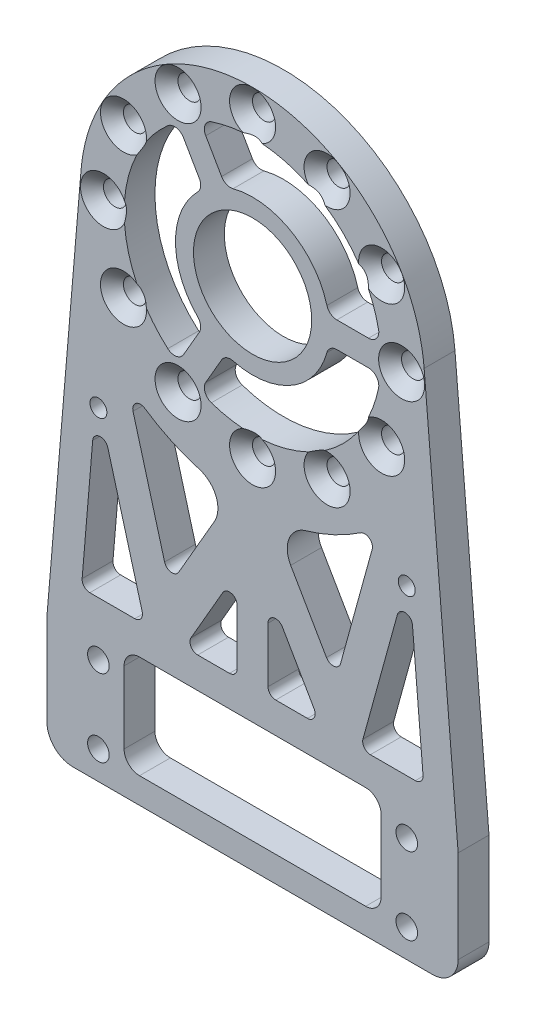
SolidWorks part; units mm, degrees
material "Thornel Mat VMA"
ref_plane "前视基准面" through (0, 0, 0) normal (0, 0, 1) x (1, 0, 0)
ref_plane "上视基准面" through (0, 0, 0) normal (0, 1, 0) x (1, 0, 0)
ref_plane "右视基准面" through (0, 0, 0) normal (1, 0, 0) x (0, 0, -1)
sketch "草图1" plane through (0, 0, 0) normal (0, 0, 1) x (1, 0, 0)
  line L0 (-40, 10) -> (-33.381, 88.3211)
  line L1 (-40, 10) -> (40, 10)
  line L2 (-40, 10) -> (-40, -10)
  line L3 (-40, -10) -> (40, -10)
  line L4 (40, 10) -> (40, -10)
  line L5 (-40, 10) -> (40, -10) construction
  line L6 (-40, -10) -> (40, 10) construction
  line L7 (-30, 7.5) -> (30, 7.5) construction
  line L8 (-30, 7.5) -> (-30, -7.5) construction
  line L9 (-30, -7.5) -> (30, -7.5) construction
  line L10 (30, 7.5) -> (30, -7.5) construction
  line L11 (-30, 7.5) -> (30, -7.5) construction
  line L12 (-30, -7.5) -> (30, 7.5) construction
  line L13 (33.381, 88.3211) -> (40, 10)
  circle A0 centre (0, 85.5) radius 33.5
  circle A1 centre (-30, -7.5) radius 2.1
  circle A2 centre (30, -7.5) radius 2.1
  circle A3 centre (30, 7.5) radius 2.1
  circle A4 centre (-30, 7.5) radius 2.1
  circle A5 centre (0, 85.5) radius 25
  point P0 (0, 0)
  point P6 (0, 0)
  dimension "D4" = 67
  dimension "D6" = 4.2
  dimension "D9" = 50
  dimension "D1" = 60
  dimension "D2" = 15
  dimension "D3" = 80
  dimension "D5" = 93
  dimension "D7" = 2
  dimension "D8" = 2
extrude "凸台-拉伸1" add sketch "草图1" along normal blind 6 contours A0 A5 | A0 L0 L1 L13 | L4 L1 L2 L3 A4 A3 A2 A1
sketch "草图3" plane through (0, 0, 6) normal (0, 0, 1) x (1, 0, 0)
  circle A0 centre (0, 85.5) radius 29 construction
  circle A1 centre (0, 114.5) radius 2.05
  circle A2 centre (14.5, 110.6147) radius 2.05
  circle A3 centre (25.1147, 100) radius 2.05
  circle A4 centre (29, 85.5) radius 2.05
  circle A5 centre (25.1147, 71) radius 2.05
  circle A6 centre (14.5, 60.3853) radius 2.05
  circle A7 centre (0, 56.5) radius 2.05
  circle A8 centre (-14.5, 60.3853) radius 2.05
  circle A9 centre (-25.1147, 71) radius 2.05
  circle A10 centre (-29, 85.5) radius 2.05
  circle A11 centre (-25.1147, 100) radius 2.05
  circle A12 centre (-14.5, 110.6147) radius 2.05
  point P29 (0, 85.5)
  dimension "D1" = 58
  dimension "D2" = 4.1
  dimension "D3" = 12
extrude "切除-拉伸1" cut sketch "草图3" against normal through all
sketch "草图4" plane through (0, 0, 6) normal (0, 0, 1) x (1, 0, 0)
  line L1 (-14.6024, 105.7921) -> (-7.7775, 93.9711)
  line L2 (-10.2723, 108.2921) -> (-3.4474, 96.4711)
  line L5 (24.8747, 83) -> (11.225, 83)
  line L6 (24.8747, 88) -> (11.225, 88)
  line L7 (-14.6024, 65.2079) -> (-7.7775, 77.0289)
  line L8 (-10.2723, 62.7079) -> (-3.4474, 74.5289)
  circle A0 centre (0, 85.5) radius 11.5
  arc A1 (-9.5602, 97.0587) -> (-9.5602, 73.9413) centre (0, 85.5) ccw
  circle A2 centre (0, 85.5) radius 25
  arc A3 (14.7902, 88) -> (-5.23, 99.5587) centre (0, 85.5) ccw
  arc A4 (-5.23, 71.4413) -> (14.7902, 83) centre (0, 85.5) ccw
  point P24 (0, 85.5)
  circle M13 centre (0, 85.5) radius 25
  dimension "D1" = 23
  dimension "D2" = 50
  dimension "D6" = 30
  dimension "D3" = 5
  dimension "D5" = 3
extrude "凸台-拉伸2" add sketch "草图4" against normal up to surface (6 mm away) separate body contours A0 L2 L1 M13 | A0 L5 L6 M13 | A0 L7 L8 M13 | L1 A1 L7 A0 | L8 A4 L5 A0 | L6 A3 L2 A0 up to face at (-23.0647, 71, 0)
combine bodies "组合1" operation type add bodies to combine 108 107
fillet "圆角1" radius 2 12 edges at (14.7902, 88, 3) (-5.23, 99.5587, 3) (24.8747, 88, 3) (-5.23, 71.4413, 3) (14.7902, 83, 3) (24.8747, 83, 3) (-10.2723, 62.7079, 3) (-10.2723, 108.2921, 3) (-9.5602, 73.9413, 3) (-14.6024, 65.2079, 3) (-9.5602, 97.0587, 3) (-14.6024, 105.7921, 3)
sketch "草图5" plane through (0, 0, 6) normal (0, 0, 1) x (1, 0, 0)
  line L1 (-40, -10) -> (40, -10)
  line L2 (-40, -10) -> (-40, -13)
  line L3 (-40, -13) -> (40, -13)
  line L4 (40, -10) -> (40, -13)
  dimension "D1" = 3
extrude "凸台-拉伸3" add sketch "草图5" against normal up to surface (6 mm away) up to face at (7.1078, 73.189, 0)
fillet "圆角2" radius 5 2 edges at (40, -13, 3) (-40, -13, 3)
sketch "草图6" plane through (0, 0, 0) normal (0, 0, -1) x (-1, 0, 0)
  line L0 (-39.3239, 18) -> (39.3239, 18)
  line L1 (-30, 7.5) -> (30, 7.5) construction
  line L2 (-30, 7.5) -> (-30, -7.5) construction
  line L3 (-30, -7.5) -> (30, -7.5) construction
  line L4 (30, 7.5) -> (30, -7.5) construction
  line L5 (-25, 12) -> (25, 12)
  line L6 (-25, 12) -> (-25, -8)
  line L7 (-25, -8) -> (25, -8)
  line L8 (25, 12) -> (25, -8)
  line L9 (-25, 12) -> (25, -8) construction
  line L10 (-25, -8) -> (25, 12) construction
  line L11 (-33.381, 88.3211) -> (-40, 10) construction
  line L12 (40, 10) -> (33.381, 88.3211) construction
  line L13 (16.1676, 26.9969) -> (26.1749, 63.3404)
  line L14 (0, 55) -> (16.1676, 26.9969)
  line L15 (34.0213, 9.4947) -> (27.4023, 87.8158)
  line L16 (34.0213, 9.4947) -> (27.4023, 87.8158)
  line L17 (0, 48) -> (-17.3205, 18)
  line L18 (-27.4023, 87.8158) -> (-34.0213, 9.4947)
  line L19 (-27.4023, 87.8158) -> (-34.0213, 9.4947)
  line L20 (0, 48) -> (17.3205, 18)
  line L21 (17.3205, 18) -> (29.5493, 62.4113)
  line L22 (-17.3205, 18) -> (-29.5493, 62.4113)
  line L23 (0, 55) -> (-16.1676, 26.9969)
  line L24 (-16.1676, 26.9969) -> (-26.1749, 63.3404)
  line L25 (19.2986, 12) -> (32.9237, 61.4821)
  line L26 (0, 41) -> (16.7432, 12)
  line L27 (0, 41) -> (-16.7432, 12)
  line L28 (18.4734, 9.0031) -> (32.9237, 61.4821) construction
  line L29 (0, 41) -> (18.4734, 9.0031) construction
  line L30 (0, 41) -> (-18.4734, 9.0031) construction
  line L31 (-19.2986, 12) -> (-32.9237, 61.4821)
  line L32 (-18.4734, 9.0031) -> (-32.9237, 61.4821) construction
  line L33 (0, 41) -> (0, 18)
  line L34 (-3, 41) -> (-3, 18)
  line L35 (3, 41) -> (3, 18)
  circle A0 centre (0, 85.5) radius 37.5
  point P4 (0, 2)
  dimension "D3" = 75
  dimension "D1" = 20
  dimension "D2" = 50
  dimension "D4" = 6
  dimension "D7" = 60
  dimension "D8" = 60
  dimension "D13" = 2
  dimension "D14" = 25
  dimension "D5" = 6
  dimension "D6" = 6
  dimension "D9" = 3.5
  dimension "D10" = 3.5
  dimension "D11" = 3
  dimension "D12" = 3
extrude "切除-拉伸2" cut sketch "草图6" against normal blind 10 contours L8 L5 L6 L7 | L0 L31 L19 | A0 L24 L23 | A0 L14 L13 | L25 L0 L16 | L34 L27 L0 | L26 L35 L0
fillet "圆角3" radius 3 4 edges at (25, -8, 3) (-25, 12, 3) (-25, -8, 3) (25, 12, 3)
fillet "圆角4" radius 1.5 16 edges at (-3, 18, 3) (-3, 35.8038, 3) (-13.2791, 18, 3) (13.2791, 18, 3) (3, 35.8038, 3) (3, 18, 3) (-16.1676, 26.9969, 3) (-24.4466, 57.0639, 3) (-33.3025, 18, 3) (-20.9508, 18, 3) (-30.4018, 52.3234, 3) (16.1676, 26.9969, 3) (24.4466, 57.0639, 3) (30.4018, 52.3234, 3) (20.9508, 18, 3) (33.3025, 18, 3)
fillet "圆角5" radius 5 2 edges at (3.9227, 48.2057, 3) (-3.9227, 48.2057, 3)
hole_wizard "M4 六角凹锥坑螺钉的锥形沉头孔1" [suppressed] positions "3D草图1" profile "草图7" countersink size "M4" standard "ISO"
sketch3d "3D草图1"
  line L3 (-14.5, 110.6147, 0) -> (-14.5, 110.6147, 6) construction
  line L7 (-14.5, 60.3853, 0) -> (-14.5, 60.3853, 6) construction
  line L11 (29, 85.5, 0) -> (29, 85.5, 6) construction
  line L12 (0, 114.5, 0) -> (0, 114.5, 6) construction
  line L13 (14.5, 110.6147, 0) -> (14.5, 110.6147, 6) construction
  line L14 (25.1147, 100, 0) -> (25.1147, 100, 6) construction
  line L15 (25.1147, 71, 0) -> (25.1147, 71, 6) construction
  line L16 (14.5, 60.3853, 0) -> (14.5, 60.3853, 6) construction
  line L17 (0, 56.5, 0) -> (0, 56.5, 6) construction
  line L18 (-25.1147, 71, 0) -> (-25.1147, 71, 6) construction
  line L19 (-29, 85.5, 0) -> (-29, 85.5, 6) construction
  line L20 (-25.1147, 100, 0) -> (-25.1147, 100, 6) construction
  point P12 (-14.5, 110.6147, 0)
  point P28 (-14.5, 60.3853, 0)
  point P44 (29, 85.5, 0)
  point P48 (0, 114.5, 0)
  point P52 (14.5, 110.6147, 0)
  point P56 (25.1147, 100, 0)
  point P60 (25.1147, 71, 0)
  point P64 (14.5, 60.3853, 0)
  point P68 (0, 56.5, 0)
  point P72 (-25.1147, 71, 0)
  point P76 (-29, 85.5, 0)
  point P80 (-25.1147, 100, 0)
sketch "草图7" plane through (-14.5, 110.6147, 0) normal (1, 0, 0) x (0, 1, 0)
  line L0 (0, 0) -> (0, 8.8519)
  line L1 (0, 8.8519) -> (2.25, 7.5)
  line L2 (2.25, 7.5) -> (2.25, 2.23)
  line L3 (2.25, 2.23) -> (4.48, 0)
  line L5 (4.48, 0) -> (0, 0)
  line L6 (-2.25, 2.23) -> (-4.48, 0) construction
  line L10 (0, 8.8519) -> (-2.25, 7.5) construction
  line L11 (0, -6.35) -> (0, 107.95) construction
  dimension "孔直径" = 4.5
  dimension "孔深度" = 7.5
  dimension "近端锥形沉头孔直径" = 8.96
  dimension "近端锥形沉头孔角度" = 90
  dimension "导头角度" = 118
hole_wizard "M4 六角凹锥坑螺钉的锥形沉头孔2" positions "草图8" profile "草图9" countersink size "M4" standard "ISO" end condition through all
sketch "草图8" plane through (0, 0, 6) normal (0, 0, 1) x (1, 0, 0)
  point P0 (-25.1147, 100)
  point P3 (-14.5, 110.6147)
  point P6 (0, 114.5)
  point P9 (14.5, 110.6147)
  point P12 (25.1147, 100)
  point P15 (29, 85.5)
  point P18 (25.1147, 71)
  point P21 (14.5, 60.3853)
  point P24 (0, 56.5)
  point P27 (-14.5, 60.3853)
  point P30 (-25.1147, 71)
  point P33 (-29, 85.5)
sketch "草图9" plane through (-25.1147, 100, 6) normal (1, 0, 0) x (0, -1, 0)
  line L0 (0, 0) -> (0, 6)
  line L1 (0, 6) -> (2.25, 6)
  line L2 (2.25, 6) -> (2.25, 2.23)
  line L3 (2.25, 2.23) -> (4.48, 0)
  line L5 (4.48, 0) -> (0, 0)
  line L6 (-2.25, 2.23) -> (-4.48, 0) construction
  line L11 (0, -6.35) -> (0, 107.95) construction
  dimension "通孔孔直径" = 4.5
  dimension "通孔孔深度" = 6
  dimension "近端锥形沉头孔直径" = 8.96
  dimension "近端锥形沉头孔角度" = 90
sketch "草图10" plane through (0, 0, 0) normal (0, 0, -1) x (-1, 0, 0)
  line L0 (30, 50) -> (-30, 50) construction
  line L1 (0, 0) -> (0, 50) construction
  circle A0 centre (30, 50) radius 1.65
  circle A1 centre (-30, 50) radius 1.65
  dimension "D1" = 3.3
  dimension "D2" = 60
  dimension "D3" = 50
extrude "切除-拉伸3" cut sketch "草图10" against normal through all
